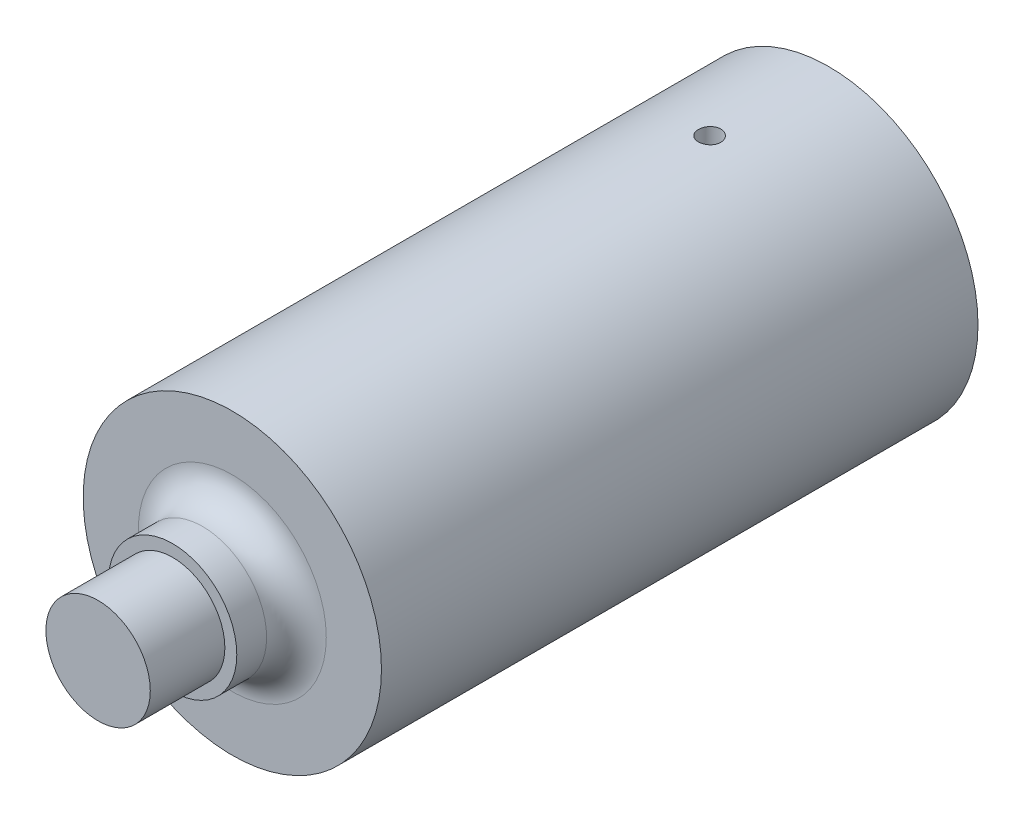
SolidWorks part; units mm, degrees
ref_plane "Plan de face" through (0, 0, 0) normal (0, 0, 1) x (1, 0, 0)
ref_plane "Plan de dessus" through (0, 0, 0) normal (0, 1, 0) x (1, 0, 0)
ref_plane "Plan de droite" through (0, 0, 0) normal (1, 0, 0) x (0, 0, -1)
sketch "Esquisse1" plane through (0, 0, 0) normal (0, 0, 1) x (1, 0, 0)
  line L0 (0, 0) -> (-13.4721, 0) construction
  line L1 (4.1569, 0) -> (2.0785, 3.6)
  line L2 (2.0785, 3.6) -> (-2.0785, 3.6)
  line L3 (-2.0785, 3.6) -> (-4.1569, 0)
  line L4 (-4.1569, 0) -> (-2.0785, -3.6)
  line L5 (-2.0785, -3.6) -> (2.0785, -3.6)
  line L6 (2.0785, -3.6) -> (4.1569, 0)
  circle A0 centre (0, 0) radius 10
  circle A2 centre (0, 0) radius 3.6 construction
  dimension "D1" = 20
  dimension "D2" = 0
  dimension "D3" = 7.2
extrude "Boss.-Extru.1" add sketch "Esquisse1" along normal blind 40
ref_plane "Plan1" through (0, 0, 0) normal (0, 1, 0) x (1, 0, 0)
sketch "Esquisse2" plane through (0, 0, 0) normal (0, 1, 0) x (1, 0, 0)
  line L0 (0, 0) -> (0, -40) construction
  line L1 (-10, -40) -> (10, -40) construction
  line L2 (0, -20) -> (19.5463, -20) construction
  circle A0 centre (0, -8) radius 0.75
  dimension "D1" = 1.5
extrude "Enlèv. mat.-Extru.1" cut sketch "Esquisse2" against normal blind 40 and the other way blind 40
sketch "Esquisse3" plane through (0, 0, 40) normal (0, 0, 1) x (1, 0, 0)
  circle A0 centre (0, 0) radius 5.2414
extrude "Boss.-Extru.2" add sketch "Esquisse3" against normal blind 20
sketch "Esquisse4" plane through (0, 0, 40) normal (0, 0, 1) x (1, 0, 0)
  circle A0 centre (0, 0) radius 3.5
  dimension "D1" = 7
extrude "Boss.-Extru.3" add sketch "Esquisse4" along normal blind 9
sketch "Esquisse5" plane through (0, 0, 40) normal (0, 0, 1) x (1, 0, 0)
  circle A0 centre (0, 0) radius 4.3
  dimension "D1" = 8.6
extrude "Boss.-Extru.4" add sketch "Esquisse5" along normal blind 4
fillet "Congé2" radius 2 1 edges at (4.3, 0, 40)
